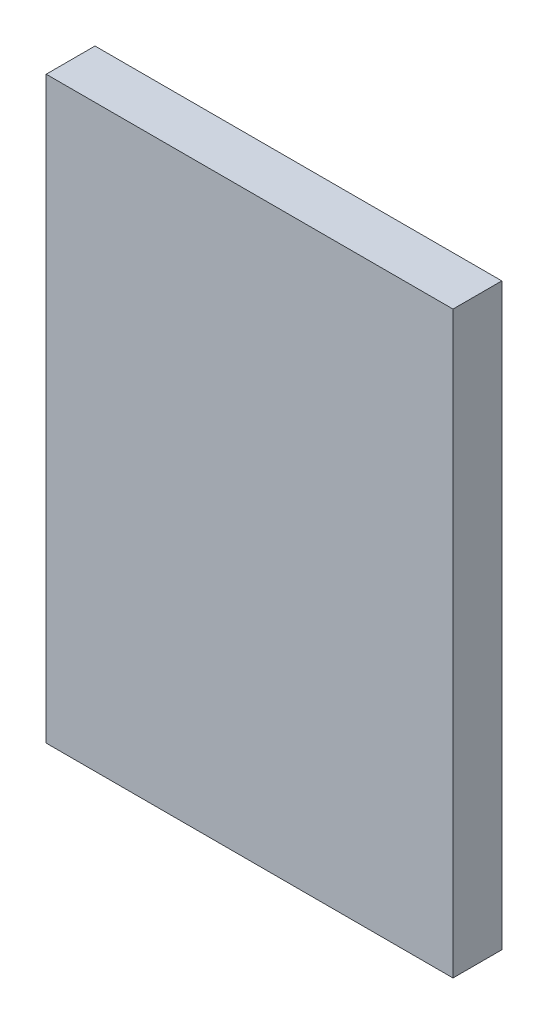
SolidWorks part; units mm, degrees
material "glass"
ref_plane "Front Plane" through (0, 0, 0) normal (0, 0, 1) x (1, 0, 0)
ref_plane "Top Plane" through (0, 0, 0) normal (0, 1, 0) x (1, 0, 0)
ref_plane "Right Plane" through (0, 0, 0) normal (1, 0, 0) x (0, 0, -1)
sketch "Sketch1" plane through (0, 0, 0) normal (0, 0, 1) x (1, 0, 0)
  line L1 (0, 0) -> (25, 0)
  line L2 (0, 0) -> (0, 35.6)
  line L3 (0, 35.6) -> (25, 35.6)
  line L4 (25, 0) -> (25, 35.6)
  dimension "D1" = 25
  dimension "D2" = 35.6
extrude "Boss-Extrude1" add sketch "Sketch1" along normal blind 3
